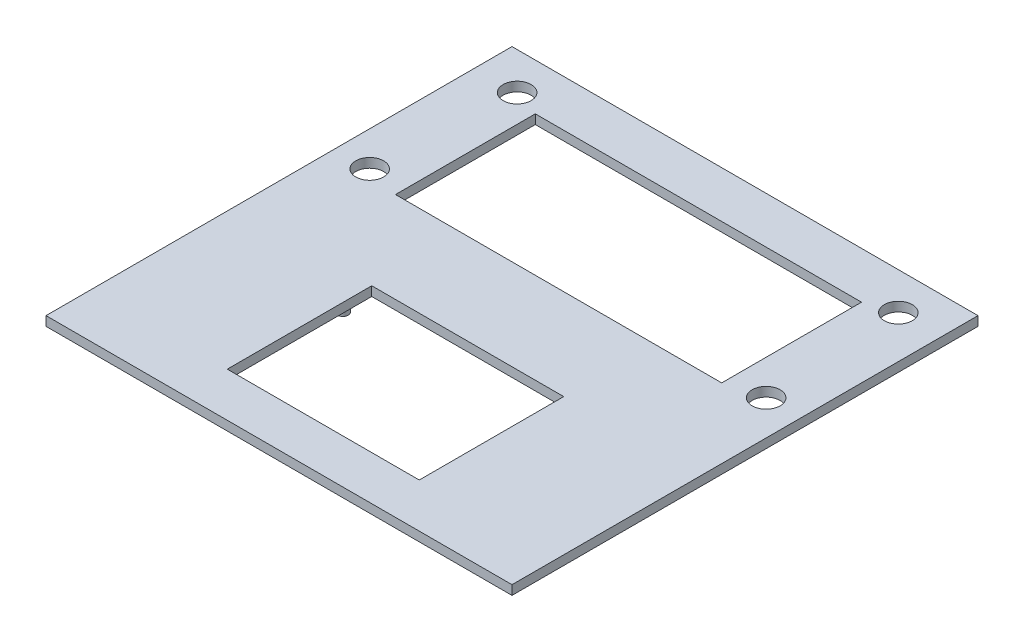
SolidWorks part; units mm, degrees
ref_plane "Front" through (0, 0, 0) normal (0, 0, 1) x (1, 0, 0)
ref_plane "Top" through (0, 0, 0) normal (0, 1, 0) x (1, 0, 0)
ref_plane "Right" through (0, 0, 0) normal (1, 0, 0) x (0, 0, -1)
sketch "Sketch1" plane through (0, 0, 0) normal (0, 1, 0) x (1, 0, 0)
  line L1 (31.75, -31.75) -> (-31.75, -31.75)
  line L2 (31.75, -31.75) -> (31.75, 31.75)
  line L3 (31.75, 31.75) -> (-31.75, 31.75)
  line L4 (-31.75, -31.75) -> (-31.75, 31.75)
  line L5 (31.75, -31.75) -> (-31.75, 31.75) construction
  line L6 (31.75, 31.75) -> (-31.75, -31.75) construction
  point P0 (0, 0)
  dimension "D1" = 63.5
  dimension "D2" = 63.5
extrude "Boss-Extrude1" add sketch "Sketch1" along normal blind 1.27
sketch "Sketch2" plane through (0, 1.27, 0) normal (0, 1, 0) x (1, 0, 0)
  line L0 (0, 31.75) -> (0, -31.75) construction
  line L1 (31.75, 31.75) -> (-31.75, 31.75) construction
  line L2 (-31.75, -31.75) -> (31.75, -31.75) construction
  line L3 (-31.75, 0) -> (31.75, 0) construction
  line L4 (-31.75, 31.75) -> (-31.75, -31.75) construction
  line L5 (31.75, -31.75) -> (31.75, 31.75) construction
  line L6 (-31.75, 31.75) -> (-31.75, 0) construction
  line L7 (-31.75, 15.875) -> (31.75, 15.875) construction
  line L8 (-25.9715, 26.67) -> (-25.9715, 31.75)
  line L9 (-25.9715, 26.67) -> (-31.75, 26.67)
  line L10 (-27.0129, 7.62) -> (-31.75, 7.62)
  line L11 (-27.0129, 7.62) -> (-27.0129, 31.75)
  circle A0 centre (-25.9715, 26.67) radius 1.905
  circle A1 centre (-27.0129, 7.62) radius 1.905
  circle A2 centre (27.0129, 7.62) radius 1.905
  circle A3 centre (25.9715, 26.67) radius 1.905
  point P16 (0, 15.875)
  point P17 (0, 0)
  dimension "D1" = 3.81
  dimension "D4" = 3.81
  dimension "D2" = 5.7785
  dimension "D3" = 5.08
  dimension "D5" = 24.13
  dimension "D6" = 4.7371
extrude "Cut-Extrude1" cut sketch "Sketch2" against normal blind 1.27 contours A2 | A3 | A1 | A0
sketch "Sketch3" plane through (0, 1.27, 0) normal (0, 1, 0) x (1, 0, 0)
  line L0 (0, 31.75) -> (0, 0) construction
  line L1 (31.75, 31.75) -> (-31.75, 31.75) construction
  line L2 (-31.75, 0) -> (31.75, 0) construction
  line L3 (-31.75, 31.75) -> (-31.75, -31.75) construction
  line L4 (31.75, -31.75) -> (31.75, 31.75) construction
  line L5 (-31.75, 0) -> (-31.75, 31.75) construction
  line L6 (31.75, 0) -> (31.75, 31.75) construction
  line L7 (-31.75, 15.875) -> (31.75, 15.875) construction
  line L9 (22.225, 6.35) -> (-22.225, 6.35)
  line L10 (22.225, 6.35) -> (22.225, 25.4)
  line L11 (22.225, 25.4) -> (-22.225, 25.4)
  line L12 (-22.225, 6.35) -> (-22.225, 25.4)
  line L13 (22.225, 6.35) -> (-22.225, 25.4) construction
  line L14 (22.225, 25.4) -> (-22.225, 6.35) construction
  point P17 (0, 15.875)
  dimension "D1" = 44.45
  dimension "D2" = 19.05
extrude "Cut-Extrude2" cut sketch "Sketch3" against normal blind 1.27
sketch "Sketch4" plane through (0, 1.27, 0) normal (0, 1, 0) x (1, 0, 0)
  line L0 (-31.75, 0) -> (31.75, 0) construction
  line L1 (-31.75, 31.75) -> (-31.75, -31.75) construction
  line L2 (31.75, -31.75) -> (31.75, 31.75) construction
  line L3 (0, 0) -> (0, -31.75) construction
  line L4 (-31.75, -31.75) -> (31.75, -31.75) construction
  line L5 (0, -15.875) -> (-31.75, -15.875) construction
  line L6 (-31.75, -15.875) -> (31.75, -15.875) construction
  line L7 (-15.748, -6.0325) -> (-15.748, -7.3025) construction
  line L12 (16.7894, -25.7175) -> (-16.7894, -6.0325) construction
  line L13 (16.7894, -6.0325) -> (-16.7894, -25.7175) construction
  line L14 (-15.748, -7.3025) -> (-16.7894, -7.3025) construction
  line L15 (15.748, -6.0325) -> (15.748, -19.3167) construction
  line L16 (15.748, -19.3167) -> (16.7894, -19.3167) construction
  circle A0 centre (-15.748, -7.3025) radius 0.7302
  circle A1 centre (15.748, -19.3167) radius 0.7303
  dimension "D7" = 1.4605
  dimension "D8" = 1.4605
  dimension "D1" = 19.685
  dimension "D2" = 33.5788
  dimension "D3" = 1.27
  dimension "D4" = 1.0414
  dimension "D5" = 13.2842
  dimension "D6" = 1.0414
extrude "Boss-Extrude2" add sketch "Sketch4" against normal blind 3.81
sketch "Sketch5" plane through (0, 1.27, 0) normal (0, 1, 0) x (1, 0, 0)
  line L1 (13.081, -25.7175) -> (-13.081, -25.7175)
  line L3 (13.081, -25.7175) -> (13.081, -6.0325)
  line L4 (0, 0) -> (0, -31.75) construction
  line L5 (13.081, -6.0325) -> (-13.081, -6.0325)
  line L6 (-13.081, -25.7175) -> (-13.081, -6.0325)
  line L7 (13.081, -25.7175) -> (-13.081, -6.0325) construction
  line L8 (13.081, -6.0325) -> (-13.081, -25.7175) construction
  point P0 (0, -15.875)
  dimension "D1" = 26.162
  dimension "D2" = 19.685
extrude "Cut-Extrude3" cut sketch "Sketch5" against normal up to next
